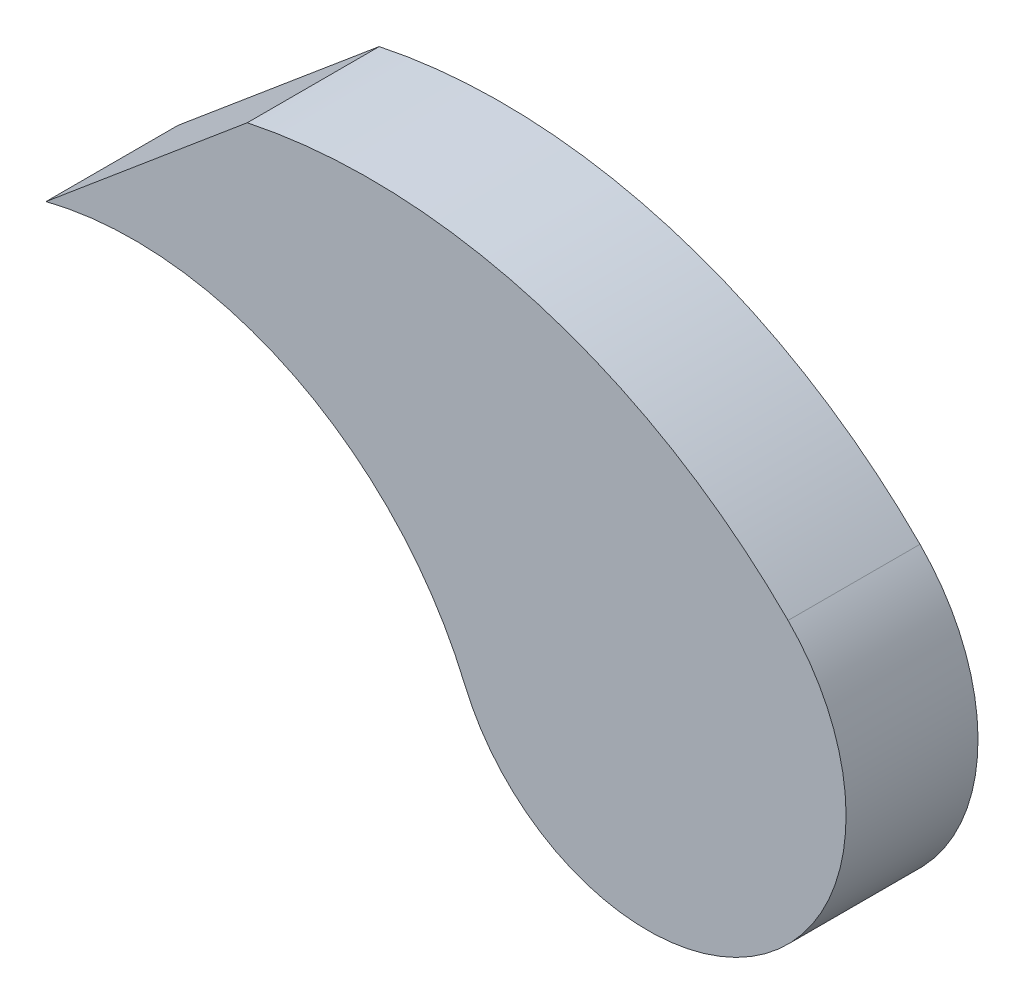
SolidWorks part; units mm, degrees
ref_plane "Front Plane" through (0, 0, 0) normal (0, 0, 1) x (1, 0, 0)
ref_plane "Top Plane" through (0, 0, 0) normal (0, 1, 0) x (1, 0, 0)
ref_plane "Right Plane" through (0, 0, 0) normal (1, 0, 0) x (0, 0, -1)
sketch "Sketch1" plane through (0, 0, 0) normal (0, 0, 1) x (1, 0, 0)
  line L0 (-9.6347, 7.239) -> (-14.478, 3.175)
  line L1 (0, 0) -> (50000, 0) construction
  arc A0 (-4.4019, -1.8508) -> (3.3792, 3.3739) centre (0, 0) ccw
  arc A1 (-4.4019, -1.8508) -> (-14.478, 3.175) centre (-12.3629, -5.198) ccw
  arc A2 (3.3792, 3.3739) -> (-9.6347, 7.239) centre (-6.6865, -6.6761) ccw
  dimension "D1" = 4.7752
  dimension "D5" = 14.224
  dimension "D6" = 8.636
  dimension "D2" = 4.064
  dimension "D3" = 3.175
  dimension "D4" = 40
  dimension "D7" = 14.478
extrude "Boss-Extrude1" add sketch "Sketch1" along normal blind 3.175
